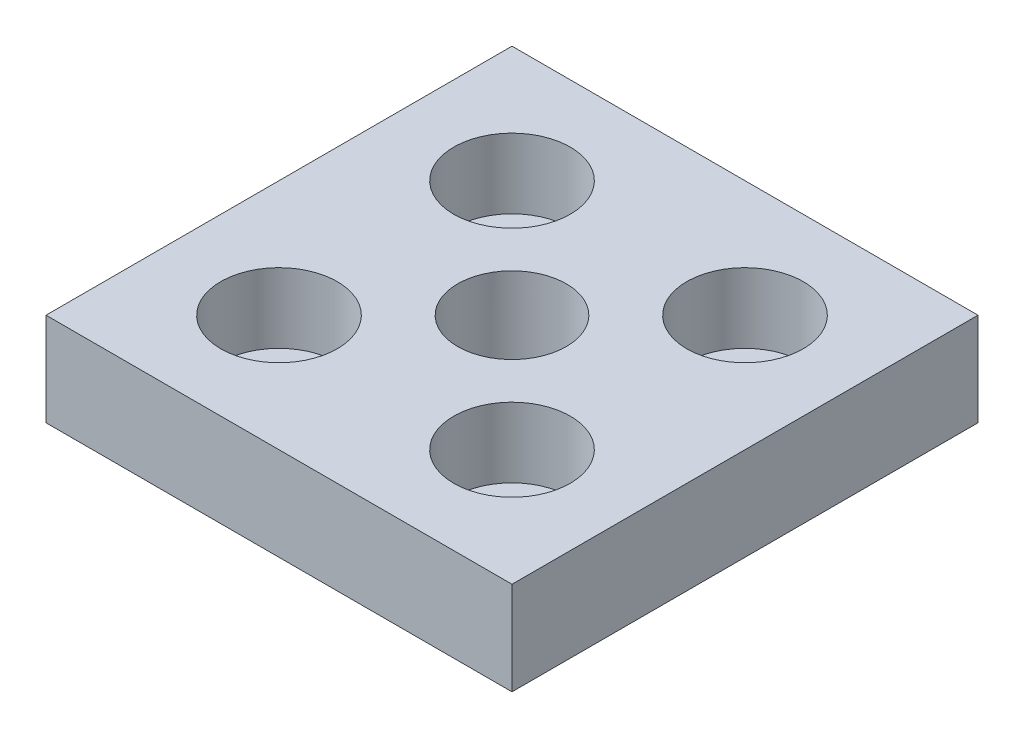
SolidWorks part; units mm, degrees
material "Алюминиевый сплав"
ref_plane "Спереди" through (0, 0, 0) normal (0, 0, 1) x (1, 0, 0)
ref_plane "Сверху" through (0, 0, 0) normal (0, 1, 0) x (1, 0, 0)
ref_plane "Справа" through (0, 0, 0) normal (1, 0, 0) x (0, 0, -1)
sketch "Эскиз1" plane through (0, 0, 0) normal (0, 1, 0) x (1, 0, 0)
  line L1 (-30, -30) -> (30, -30)
  line L2 (-30, -30) -> (-30, 30)
  line L3 (-30, 30) -> (30, 30)
  line L4 (30, -30) -> (30, 30)
  line L5 (-30, -30) -> (30, 30) construction
  line L6 (-30, 30) -> (30, -30) construction
  point P0 (0, 0)
  dimension "D1" = 60
extrude "Бобышка-Вытянуть1" add sketch "Эскиз1" along normal blind 12
hole_wizard "Отверстие обработанное метчиком M161" positions "Эскиз6" profile "Эскиз7" tap size "M16" standard "ISO" end condition up to next
sketch "Эскиз6" plane through (0, 12, 0) normal (0, 1, 0) x (1, 0, 0)
  point P0 (0, 0)
sketch "Эскиз7" plane through (0, 12, 0) normal (1, 0, 0) x (0, 0, 1)
  line L0 (0, 0) -> (0, 12)
  line L1 (0, 12) -> (7, 12)
  line L2 (7, 12) -> (7, 0)
  line L5 (7, 0) -> (0, 0)
  line L11 (0, -6.35) -> (0, 107.95) construction
  dimension "Диаметр проходного сверла" = 14
  dimension "Глубина проходного сверла" = 12
cosmetic thread "Отверстие резьбы2" parameters "D2"=16
sketch "Эскиз12" plane through (0, 12, 0) normal (0, 1, 0) x (1, 0, 0)
  line L1 (15, -15) -> (-15, -15) construction
  line L2 (15, -15) -> (15, 15) construction
  line L3 (15, 15) -> (-15, 15) construction
  line L4 (-15, -15) -> (-15, 15) construction
  line L5 (15, -15) -> (-15, 15) construction
  line L6 (15, 15) -> (-15, -15) construction
  circle A0 centre (-15, 15) radius 4.5
  circle A1 centre (15, 15) radius 4.5
  circle A2 centre (15, -15) radius 4.5
  circle A3 centre (-15, -15) radius 4.5
  point P0 (0, 0)
  dimension "D2" = 9
  dimension "D1" = 30
extrude "Вырез-Вытянуть1" cut sketch "Эскиз12" against normal through all
sketch "Эскиз13" plane through (0, 12, 0) normal (0, 1, 0) x (1, 0, 0)
  circle A0 centre (-15, 15) radius 7.5
  circle A1 centre (15, 15) radius 7.5
  circle A2 centre (15, -15) radius 7.5
  circle A3 centre (-15, -15) radius 7.5
  dimension "D1" = 15
extrude "Вырез-Вытянуть2" cut sketch "Эскиз13" against normal blind 9
